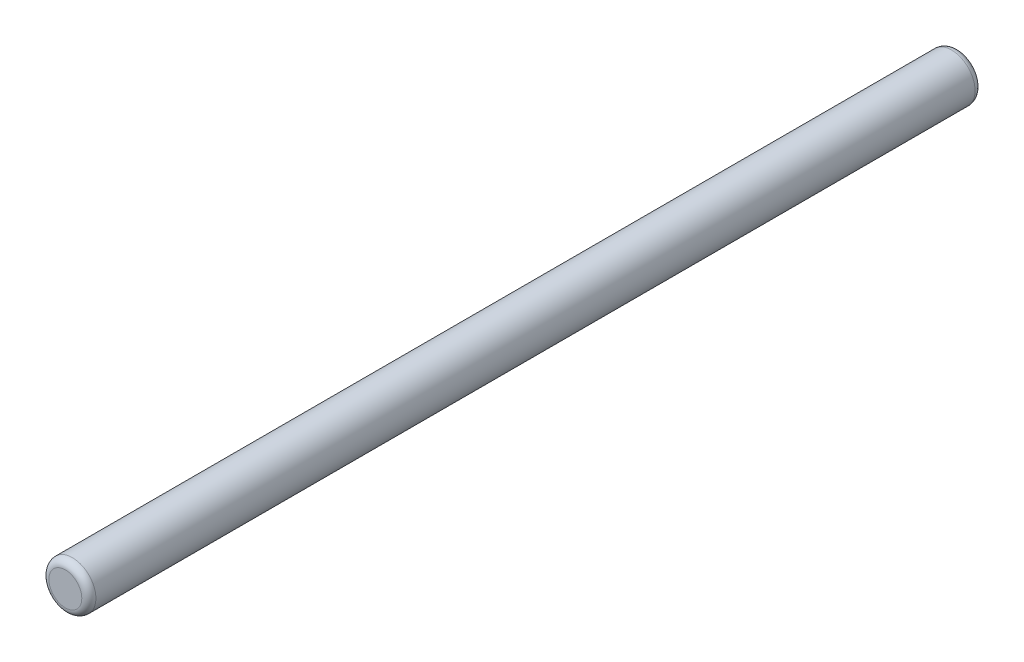
SolidWorks part; units mm, degrees
ref_plane "Face" through (0, 0, 0) normal (0, 0, 1) x (1, 0, 0)
ref_plane "Dessus" through (0, 0, 0) normal (0, 1, 0) x (1, 0, 0)
ref_plane "Droite" through (0, 0, 0) normal (1, 0, 0) x (0, 0, -1)
sketch "Esquisse1" plane through (0, 0, 0) normal (0, 0, 1) x (1, 0, 0)
  circle A0 centre (0, 0) radius 1
extrude "Base-Extrusion" add sketch "Esquisse1" along normal blind 38
fillet "Congé1" radius 0.3
